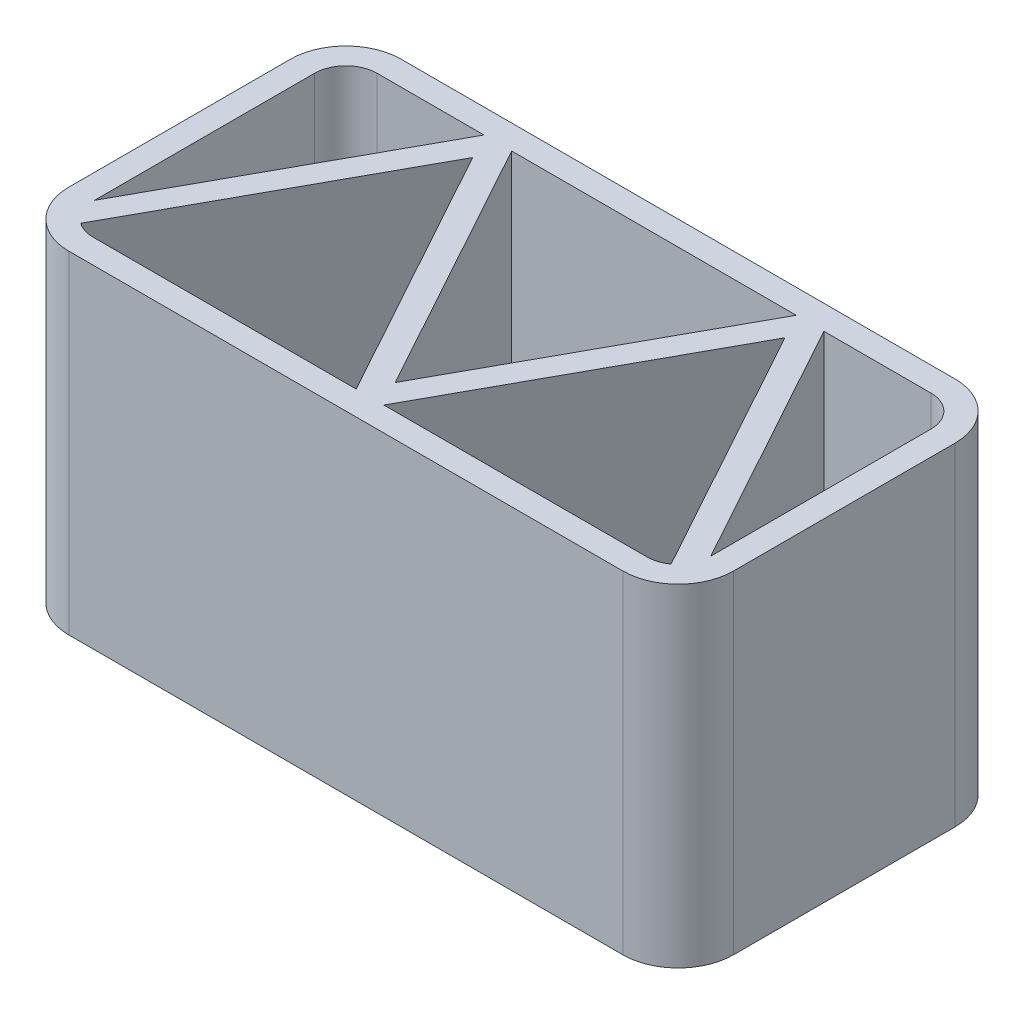
SolidWorks part; units mm, degrees
ref_plane "Front Plane" through (0, 0, 0) normal (0, 0, 1) x (1, 0, 0)
ref_plane "Top Plane" through (0, 0, 0) normal (0, 1, 0) x (1, 0, 0)
ref_plane "Right Plane" through (0, 0, 0) normal (1, 0, 0) x (0, 0, -1)
sketch "Sketch1" plane through (0, 0, 0) normal (0, 1, 0) x (1, 0, 0)
  line L1 (-254, 152.4) -> (254, 152.4)
  line L2 (-304.8, 101.6) -> (-304.8, -101.6)
  line L3 (-254, -152.4) -> (254, -152.4)
  line L4 (304.8, 101.6) -> (304.8, -101.6)
  line L5 (-304.8, 152.4) -> (304.8, -152.4) construction
  line L6 (-304.8, -152.4) -> (304.8, 152.4) construction
  arc A0 (254, 152.4) -> (304.8, 101.6) centre (254, 101.6) cw
  arc A1 (254, -152.4) -> (304.8, -101.6) centre (254, -101.6) ccw
  arc A2 (-304.8, -101.6) -> (-254, -152.4) centre (-254, -101.6) ccw
  arc A3 (-254, 152.4) -> (-304.8, 101.6) centre (-254, 101.6) ccw
  point P0 (0, 0)
  dimension "D3" = 50.8
  dimension "D1" = 609.6
  dimension "D2" = 304.8
extrude "Extrude-Thin1" add sketch "Sketch1" along normal blind 304.8 thin
sketch "Sketch2" plane through (0, 304.8, 0) normal (0, 1, 0) x (1, 0, 0)
  line L0 (-286.2966, -130.175) -> (-145.374, 126.1269)
  line L1 (254, 130.175) -> (-254, 130.175) construction
  line L2 (-286.2966, -130.175) -> (0, -130.175) construction
  line L3 (-140.9225, 126.1269) -> (-2.2257, -126.1269)
  line L4 (-254, -130.175) -> (254, -130.175) construction
  line L5 (286.2966, -130.175) -> (0, -130.175) construction
  line L6 (2.2257, -126.1269) -> (140.9225, 126.1269)
  line L7 (145.374, 126.1269) -> (286.2966, -130.175)
  line L8 (-143.1483, 130.175) -> (143.1483, 130.175) construction
  arc A0 (-145.374, 126.1269) -> (-140.9225, 126.1269) centre (-143.1483, 124.9032) cw
  arc A1 (140.9225, 126.1269) -> (145.374, 126.1269) centre (143.1483, 124.9032) cw
  arc A2 (-2.2257, -126.1269) -> (2.2257, -126.1269) centre (0, -124.9032) ccw
  dimension "D1" = 2.54
extrude "Extrude-Thin3" add sketch "Sketch2" against normal up to vertex (304.8 mm away) thin
